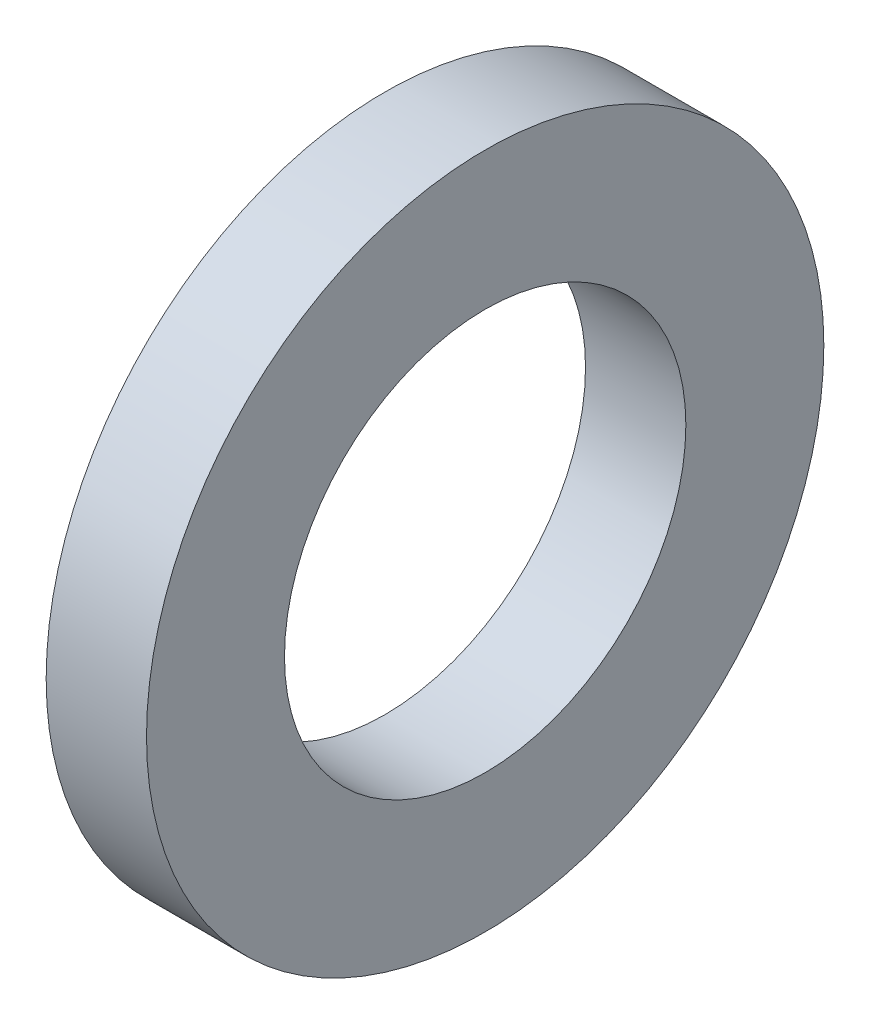
SolidWorks part; units mm, degrees
material "Pine"
ref_plane "Front Plane" through (0, 0, 0) normal (0, 0, 1) x (1, 0, 0)
ref_plane "Top Plane" through (0, 0, 0) normal (0, 1, 0) x (1, 0, 0)
ref_plane "Right Plane" through (0, 0, 0) normal (1, 0, 0) x (0, 0, -1)
sketch "Sketch1" plane through (0, 0, 0) normal (1, 0, 0) x (0, 0, -1)
  circle A0 centre (0, 0) radius 6.75
  dimension "D1" = 13.5
extrude "Boss-Extrude1" add sketch "Sketch1" along normal blind 2
sketch "Sketch2" plane through (2, 0, 0) normal (1, 0, 0) x (0, 0, -1)
  circle A0 centre (0, 0) radius 4
  dimension "D1" = 8
extrude "Cut-Extrude1" cut sketch "Sketch2" against normal through all
